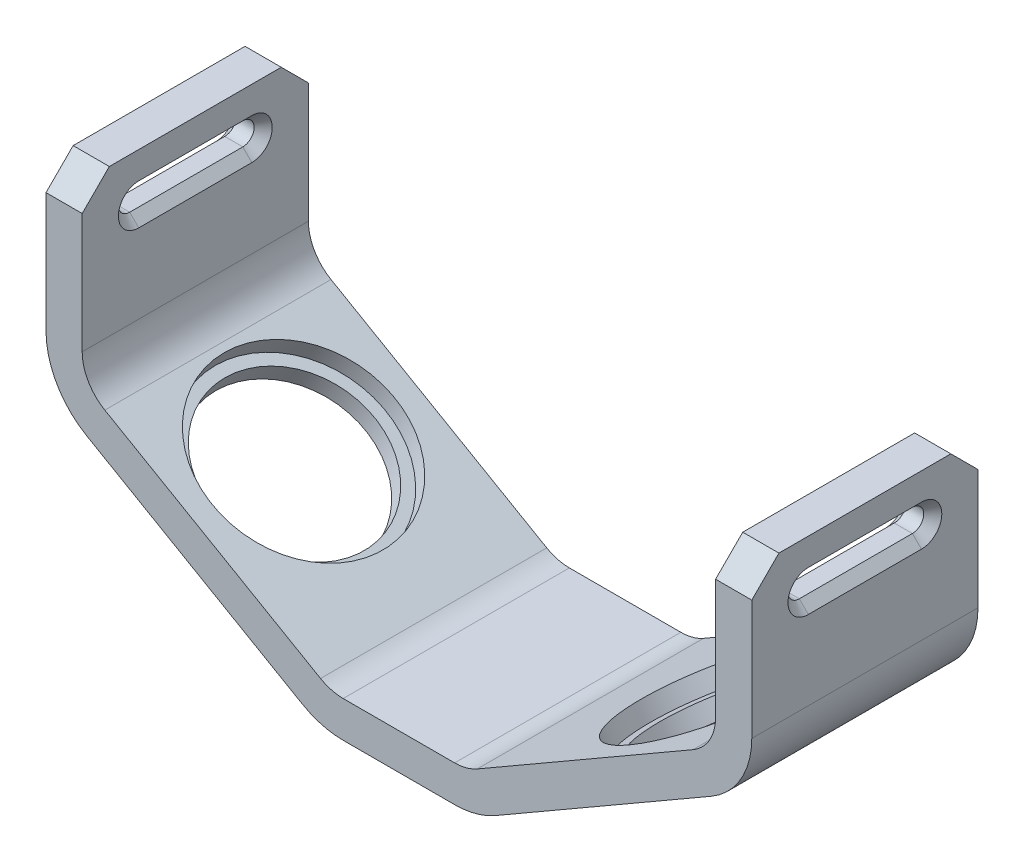
SolidWorks part; units mm, degrees
ref_plane "Front Plane" through (0, 0, 0) normal (0, 0, 1) x (1, 0, 0)
ref_plane "Top Plane" through (0, 0, 0) normal (0, 1, 0) x (1, 0, 0)
ref_plane "Right Plane" through (0, 0, 0) normal (1, 0, 0) x (0, 0, -1)
sketch "Sketch1" plane through (0, 0, 0) normal (0, 0, 1) x (1, 0, 0)
  line L0 (-15, 0) -> (15, 0)
  line L1 (15, 0) -> (70, 31.7543)
  line L2 (-15, 0) -> (-70, 31.7543)
  line L8 (-39, 13.8564) -> (-11.5, 61.4878) construction
  line L9 (39, 13.8564) -> (11.5, 61.4878) construction
  line L10 (-70, 31.7543) -> (-70, 70)
  line L11 (70, 31.7543) -> (70, 70)
  line L12 (78, 27.1355) -> (78, 70)
  line L13 (17.1436, -8) -> (78, 27.1355)
  line L14 (-17.1436, -8) -> (17.1436, -8)
  line L15 (-17.1436, -8) -> (-78, 27.1355)
  line L16 (-78, 27.1355) -> (-78, 70)
  line L17 (-78, 70) -> (-70, 70)
  line L18 (70, 70) -> (78, 70)
  point P2 (0, 0)
  dimension "D1" = 30
  dimension "D2" = 140
  dimension "D3" = 120
  dimension "D5" = 78
  dimension "D6" = 8
  dimension "D7" = 55
  dimension "D8" = 55
  dimension "D4" = 70
extrude "Boss-Extrude1" add sketch "Sketch1" along normal blind 50
fillet "Fillet1" radius 10 4 edges at (15, 0, 25) (-15, 0, 25) (70, 31.7543, 25) (-70, 31.7543, 25)
fillet "Fillet2" radius 18 4 edges at (78, 27.1355, 25) (17.1436, -8, 25) (-17.1436, -8, 25) (-78, 27.1355, 25)
sketch "Sketch2" plane through (-78, 160.7531, 0) normal (1, 0, 0) x (0, 0, 1)
  line L0 (12.5, 101.2531) -> (37.5, 101.2531) construction
  line L1 (12.5, 103.7531) -> (37.5, 103.7531)
  line L2 (12.5, 98.7531) -> (37.5, 98.7531)
  line L4 (50, 90.7531) -> (0, 90.7531) construction
  arc A0 (12.5, 103.7531) -> (12.5, 98.7531) centre (12.5, 101.2531) ccw
  arc A1 (37.5, 98.7531) -> (37.5, 103.7531) centre (37.5, 101.2531) ccw
  point P2 (25, 101.2531)
  point P9 (25, 90.7531)
  dimension "D1" = 25
  dimension "D2" = 5
  dimension "D3" = 8
extrude "Cut-Extrude1" cut sketch "Sketch2" along normal up to next (8 mm away)
chamfer "Chamfer1" distance 2 angle 45 8 edges at (-78, 62, 25) (-78, 59.5, 40) (-78, 59.5, 10) (-78, 57, 25) (-70, 62, 25) (-70, 59.5, 10) (-70, 59.5, 40) (-70, 57, 25)
chamfer "Chamfer2" distance 6 angle 45 2 edges at (-74, 70, 0) (-74, 70, 50)
sketch "Sketch3" plane through (-27.3501, -2.1073, 0) normal (0.5, 0.866, 0) x (0, 0, 1)
  line L1 (44, -79.9178) -> (6, -79.9178) construction
  line L2 (50, 6.9623) -> (0, 6.9623) construction
  circle A0 centre (25, -26.2377) radius 17.75
  point P6 (25, -79.9178)
  dimension "D1" = 35.5
  dimension "D2" = 33.2
extrude "Cut-Extrude2" cut sketch "Sketch3" along normal up to next (8 mm away)
sketch "Sketch4" plane through (-3.75, -6.4952, 0) normal (0.5, 0.866, 0) x (0, 0, -1)
  circle A0 centre (-25, 48.8699) radius 20.25
  dimension "D1" = 40.5
extrude "Cut-Extrude3" cut sketch "Sketch4" against normal blind 4
mirror "Mirror2" about plane through (0, 0, 0) normal (1, 0, 0) of "Cut-Extrude3", "Cut-Extrude1", "Chamfer1", "Chamfer2", "Cut-Extrude2"
